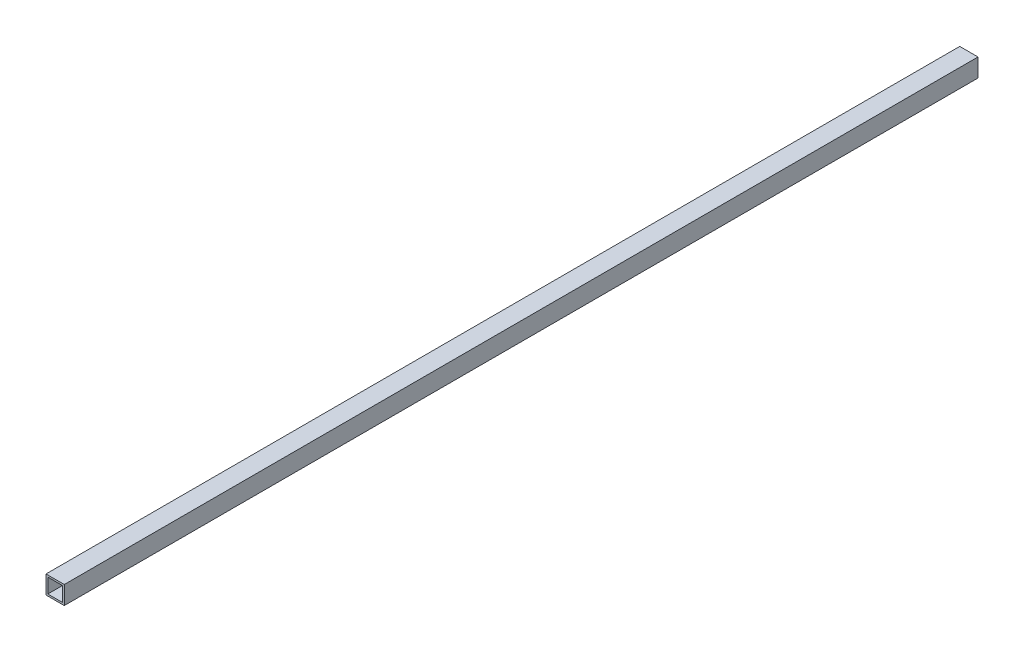
SolidWorks part; units mm, degrees
material "Alaşım Çelik"
ref_plane "Ön Düzlem" through (0, 0, 0) normal (0, 0, 1) x (1, 0, 0)
ref_plane "Üst Düzlem" through (0, 0, 0) normal (0, 1, 0) x (1, 0, 0)
ref_plane "Sağ Düzlem" through (0, 0, 0) normal (1, 0, 0) x (0, 0, -1)
sketch "Çizim1" plane through (0, 0, 0) normal (0, 0, 1) x (1, 0, 0)
  line L1 (0, 0) -> (40, 0)
  line L2 (0, 0) -> (0, 40)
  line L3 (0, 40) -> (40, 40)
  line L4 (40, 0) -> (40, 40)
  line L5 (4, 4) -> (36, 4)
  line L6 (4, 4) -> (4, 36)
  line L7 (4, 36) -> (36, 36)
  line L8 (36, 4) -> (36, 36)
  dimension "D1" = 40
  dimension "D2" = 40
  dimension "D3" = 4
  dimension "D4" = 4
  dimension "D5" = 4
  dimension "D6" = 4
extrude "Yükseklik-Ekstrüzyon1" add sketch "Çizim1" against normal blind 2000
